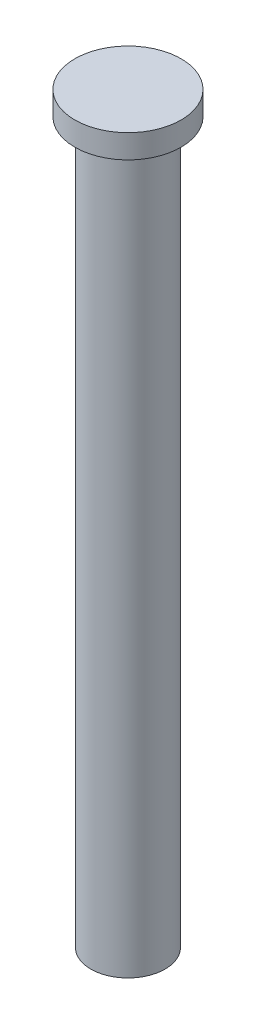
SolidWorks part; units mm, degrees
ref_plane "Plan de face" through (0, 0, 0) normal (0, 0, 1) x (1, 0, 0)
ref_plane "Plan de dessus" through (0, 0, 0) normal (0, 1, 0) x (1, 0, 0)
ref_plane "Plan de droite" through (0, 0, 0) normal (1, 0, 0) x (0, 0, -1)
sketch "Esquisse1" plane through (0, 0, 0) normal (0, 1, 0) x (1, 0, 0)
  circle A0 centre (0, 0) radius 3.15
  dimension "D1" = 6.3
extrude "Boss.-Extru.1" add sketch "Esquisse1" along normal blind 61
sketch "Esquisse3" plane through (0, 61, 0) normal (0, 1, 0) x (1, 0, 0)
  circle A0 centre (0, 0) radius 4.5
  dimension "D1" = 9
extrude "Boss.-Extru.2" add sketch "Esquisse3" along normal blind 2
